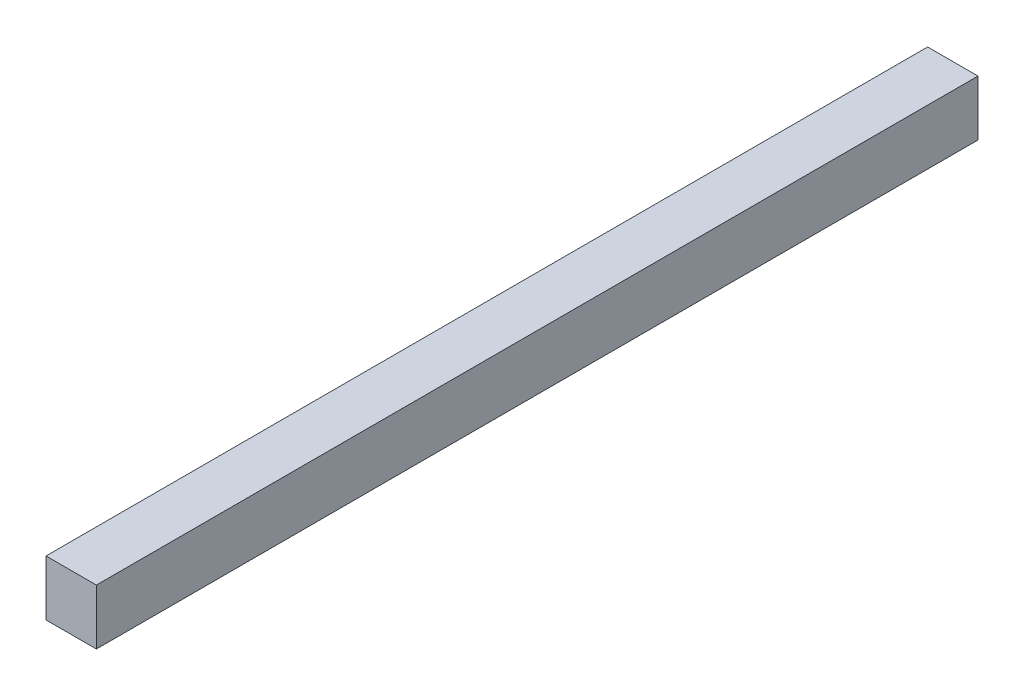
SolidWorks part; units mm, degrees
ref_plane "前视基准面" through (0, 0, 0) normal (0, 0, 1) x (1, 0, 0)
ref_plane "上视基准面" through (0, 0, 0) normal (0, 1, 0) x (1, 0, 0)
ref_plane "右视基准面" through (0, 0, 0) normal (1, 0, 0) x (0, 0, -1)
sketch "草图1" plane through (0, 0, 0) normal (0, 0, 1) x (1, 0, 0)
  line L1 (0, 0) -> (2, 0)
  line L2 (0, 0) -> (0, -2.2)
  line L3 (0, -2.2) -> (2, -2.2)
  line L4 (2, 0) -> (2, -2.2)
  dimension "D1" = 2
  dimension "D2" = 2.2
extrude "凸台-拉伸1" add sketch "草图1" along normal blind 35
